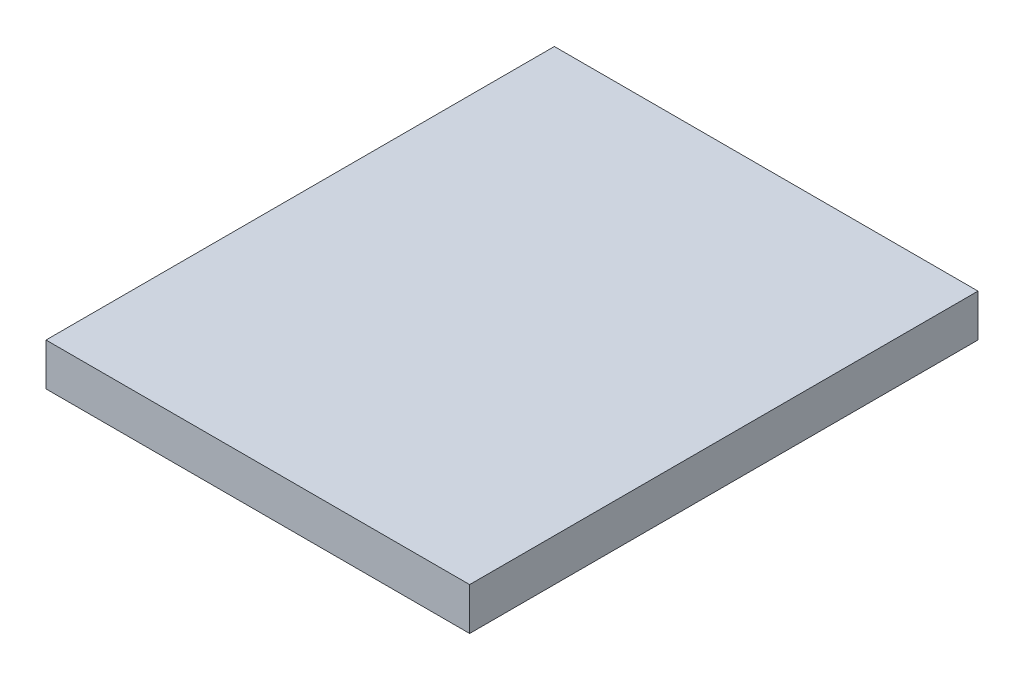
SolidWorks part; units mm, degrees
ref_plane "Front Plane" through (0, 0, 0) normal (0, 0, 1) x (1, 0, 0)
ref_plane "Top Plane" through (0, 0, 0) normal (0, 1, 0) x (1, 0, 0)
ref_plane "Right Plane" through (0, 0, 0) normal (1, 0, 0) x (0, 0, -1)
sketch "Sketch1" plane through (0, 0, 0) normal (0, 1, 0) x (1, 0, 0)
  line L1 (0, 0) -> (15.875, 0)
  line L2 (0, 0) -> (0, 19.05)
  line L3 (0, 19.05) -> (15.875, 19.05)
  line L4 (15.875, 0) -> (15.875, 19.05)
  dimension "D1" = 15.875
  dimension "D2" = 19.05
extrude "Boss-Extrude1" add sketch "Sketch1" along normal blind 1.5875
